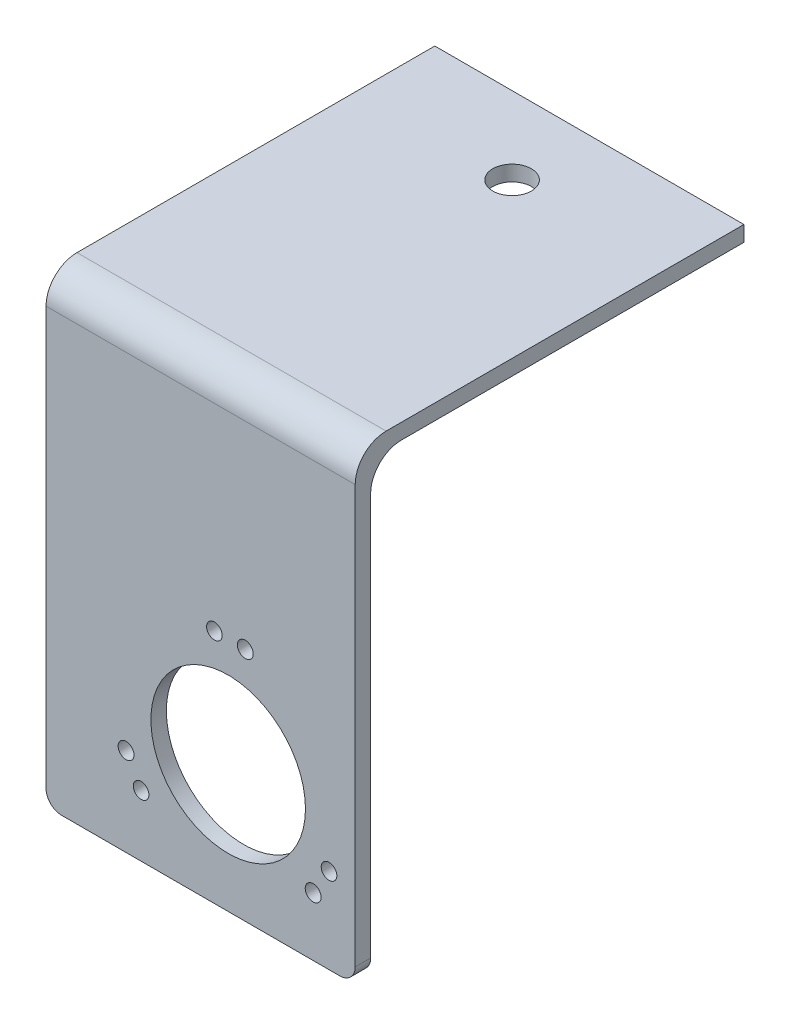
SolidWorks part; units mm, degrees
ref_plane "Front Plane" through (0, 0, 0) normal (0, 0, 1) x (1, 0, 0)
ref_plane "Top Plane" through (0, 0, 0) normal (0, 1, 0) x (1, 0, 0)
ref_plane "Right Plane" through (0, 0, 0) normal (1, 0, 0) x (0, 0, -1)
sketch "Sketch1" plane through (0, 0, 0) normal (0, 0, 1) x (1, 0, 0)
  line L1 (-20, -21) -> (20, -21)
  line L2 (-20, -21) -> (-20, 21)
  line L3 (-20, 21) -> (20, 21)
  line L4 (20, -21) -> (20, 21)
  line L5 (0, 21) -> (0, -21) construction
  line L6 (-20, 0) -> (20, 0) construction
  point P0 (0, 0)
  dimension "D1" = 40
  dimension "D2" = 42
extrude "Boss-Extrude1" add sketch "Sketch1" along normal blind 2
sketch "Sketch3" plane through (0, 0, 0) normal (0, 0, -1) x (-1, 0, 0)
  line L0 (20, 21) -> (20, -21) construction
  line L1 (-20, 21) -> (20, 21)
  line L2 (-20, 21) -> (-20, 19)
  line L3 (-20, 19) -> (20, 19)
  line L4 (20, 21) -> (20, 19)
  dimension "D1" = 2
extrude "Boss-Extrude2" add sketch "Sketch3" along normal up to vertex (48.3 mm away)
fillet "Fillet1" radius 2 2 edges at (0, 21, 2) (0, 19, 0)
fillet "Fillet2" radius 2 2 edges at (20, -21, 1) (-20, -21, 1)
sketch "Sketch4" plane through (0, 19, 0) normal (0, -1, 0) x (1, 0, 0)
  line L0 (0, -48.3) -> (0, -38.3) construction
  line L1 (20, -48.3) -> (-20, -48.3) construction
  circle A0 centre (0, -38.3) radius 2.5
  dimension "D2" = 5
  dimension "D1" = 10
sketch "Sketch6" plane through (0, 0, 2) normal (0, 0, 1) x (1, 0, 0)
  line L4 (-18, -21) -> (18, -21)
  line L5 (20, -19) -> (20, 19)
  line L6 (20, 19) -> (-20, 19)
  line L7 (-20, 19) -> (-20, -19)
  line L8 (-18, -21) -> (18, -21)
  line L9 (20, -19) -> (20, 19)
  line L10 (20, 19) -> (-20, 19)
  line L11 (-20, 19) -> (-20, -19)
  arc A2 (18, -21) -> (20, -19) centre (18, -19) ccw
  arc A3 (-20, -19) -> (-18, -21) centre (-18, -19) ccw
  arc A4 (18, -21) -> (20, -19) centre (18, -19) ccw
  arc A5 (-20, -19) -> (-18, -21) centre (-18, -19) ccw
  dimension "D1" = 0
sketch "Sketch7" plane through (0, 0, 2) normal (0, 0, 1) x (1, 0, 0)
  circle A2 centre (-7.7003, -13.0624) radius 1.0085 construction
  circle A3 centre (-9.6463, -9.5677) radius 1.0263 construction
  circle A4 centre (1.7825, 9.5373) radius 1.0085 construction
  circle A5 centre (5.7821, 9.4752) radius 1.0263 construction
  circle A6 centre (-7.7003, -13.0624) radius 1.0085
  circle A7 centre (-9.6463, -9.5677) radius 1.0263
  circle A8 centre (1.7825, 9.5373) radius 1.0085
  circle A9 centre (5.7821, 9.4752) radius 1.0263
  circle A10 centre (3.5651, -4.5) radius 10 construction
  circle A11 centre (3.5651, -4.5) radius 10
  circle A12 centre (16.613, -9.9749) radius 1.0085 construction
  circle A13 centre (14.5595, -13.4076) radius 1.0263 construction
  circle A14 centre (16.613, -9.9749) radius 1.0085
  circle A15 centre (14.5595, -13.4076) radius 1.0263
extrude "Cut-Extrude5" cut sketch "Sketch7" against normal up to next
extrude "Cut-Extrude6" cut sketch "Sketch4" against normal up to next
sketch "Sketch8" plane through (0, 21, 0) normal (0, 1, 0) x (1, 0, 0)
  line L0 (20, -2) -> (-20, -2) construction
  line L5 (-20, 48.3) -> (20, 48.3)
  line L6 (-20, 48.3) -> (-20, -2)
  line L7 (-20, -2) -> (20, -2)
  line L8 (20, 48.3) -> (20, -2)
  circle A0 centre (0, 38.3) radius 2.5
extrude "Boss-Extrude3" add sketch "Sketch8" along normal blind 18.05
sketch "Sketch10" plane through (0, 0, 2) normal (0, 0, 1) x (1, 0, 0)
  line L0 (-20, 39.05) -> (-20, 21) construction
  line L1 (-20, 25.7486) -> (20, 25.7486)
  line L2 (-20, 25.7486) -> (-20, 19)
  line L3 (-20, 19) -> (20, 19)
  line L4 (20, 25.7486) -> (20, 19)
  line L5 (20, 19) -> (20, 21) construction
  line L6 (20, 19) -> (-20, 19) construction
extrude "Boss-Extrude5" add sketch "Sketch10" against normal blind 17.05
sketch "Sketch11" plane through (0, 19, 0) normal (0, -1, 0) x (1, 0, 0)
  line L1 (-20, -2) -> (20, -2)
  line L2 (-20, -2) -> (-20, -48.3)
  line L3 (-20, -48.3) -> (20, -48.3)
  line L4 (20, -2) -> (20, -48.3)
extrude "Cut-Extrude7" cut sketch "Sketch11" against normal blind 18.05
sketch "Sketch12" plane through (0, 39.05, 0) normal (0, 1, 0) x (1, 0, 0)
  line L0 (-20, 2) -> (-20, 0) construction
  line L1 (-20, 0) -> (20, 0)
  line L2 (-20, 0) -> (-20, 2)
  line L3 (-20, 2) -> (20, 2)
  line L4 (20, 0) -> (20, 2)
extrude "Cut-Extrude8" cut sketch "Sketch12" against normal blind 22.05
sketch "Sketch13" plane through (20, 0, 0) normal (1, 0, 0) x (0, 0, -1)
  line L0 (48.3, 37.05) -> (2, 37.05) construction
  line L1 (0, 39.05) -> (2, 39.05)
  line L2 (0, 39.05) -> (0, 37.05)
  line L3 (0, 37.05) -> (2, 37.05)
  line L4 (2, 39.05) -> (2, 37.05)
extrude "Boss-Extrude6" add sketch "Sketch13" against normal blind 40
fillet "Fillet3" radius 4 1 edges at (0, 39.05, 2)
fillet "Fillet4" radius 4 1 edges at (0, 37.05, 0)
